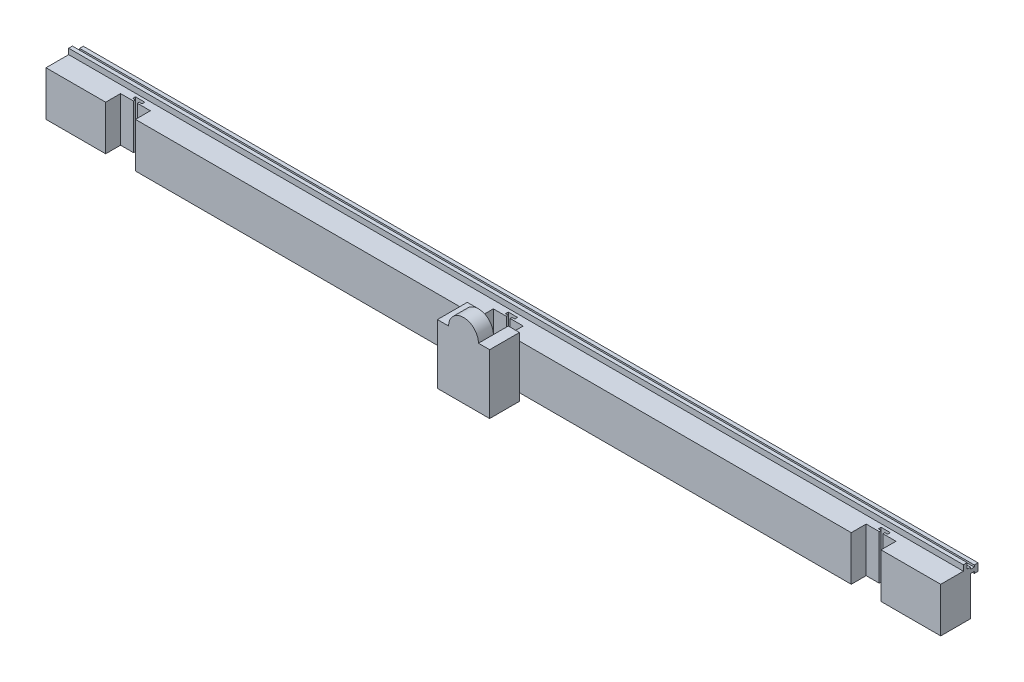
SolidWorks part; units mm, degrees
material "Plain Carbon Steel"
ref_plane "Front Plane" through (0, 0, 0) normal (0, 0, 1) x (1, 0, 0)
ref_plane "Top Plane" through (0, 0, 0) normal (0, 1, 0) x (1, 0, 0)
ref_plane "Right Plane" through (0, 0, 0) normal (1, 0, 0) x (0, 0, -1)
sketch "Sketch2" plane through (0, 0, 0) normal (0, 0, 1) x (1, 0, 0)
  line L1 (-3048, -152.4) -> (3048, -152.4)
  line L2 (-3048, -152.4) -> (-3048, 152.4)
  line L3 (-3048, 152.4) -> (3048, 152.4)
  line L4 (3048, -152.4) -> (3048, 152.4)
  line L5 (-3048, -152.4) -> (3048, 152.4) construction
  line L6 (-3048, 152.4) -> (3048, -152.4) construction
  point P0 (0, 0)
  dimension "D1" = 6096
  dimension "D2" = 304.8
extrude "Boss-Extrude1" add sketch "Sketch2" against normal blind 203.2
sketch "Sketch4" plane through (0, 152.4, 0) normal (0, 1, 0) x (1, 0, 0)
  line L0 (3048, 0) -> (-3048, 0) construction
  line L1 (-75.8517, 0) -> (75.8517, 0)
  line L2 (-75.8517, 0) -> (-75.8517, 101.6)
  line L3 (-75.8517, 101.6) -> (-12.7, 101.6)
  line L4 (75.8517, 0) -> (75.8517, 101.6)
  line L7 (-31.75, 114.3) -> (-12.7, 114.3)
  line L9 (-31.75, 114.3) -> (-31.75, 133.35)
  line L10 (-31.75, 133.35) -> (31.75, 133.35)
  line L11 (31.75, 114.3) -> (31.75, 133.35)
  line L14 (-12.7, 114.3) -> (-12.7, 101.6)
  line L16 (12.7, 114.3) -> (12.7, 101.6)
  line L17 (31.75, 114.3) -> (12.7, 114.3)
  line L18 (12.7, 101.6) -> (75.8517, 101.6)
  point P0 (0, 32.5425)
  point P11 (0, 101.6)
  dimension "D1" = 101.6
  dimension "D2" = 63.5
  dimension "D3" = 151.7034
  dimension "D5" = 19.05
extrude "Cut-Extrude1" cut sketch "Sketch4" against normal through all
pattern_linear "LPattern1" count 2 spacing 2540 along (-1, 0, 0) count 2 spacing 2540 along (1, 0, 0) of "Cut-Extrude1"
sketch "Sketch5" plane through (0, 152.4, 0) normal (0, 1, 0) x (1, 0, 0)
  line L0 (3048, 203.2) -> (3048, 0) construction
  line L1 (-3048, 179.8606) -> (3048, 179.8606)
  line L2 (-3048, 179.8606) -> (-3048, 154.4606)
  line L3 (-3048, 154.4606) -> (3048, 154.4606)
  line L4 (3048, 179.8606) -> (3048, 154.4606)
  line L5 (-3048, 179.8606) -> (3048, 154.4606) construction
  line L6 (-3048, 154.4606) -> (3048, 179.8606) construction
  point P0 (0, 167.1606)
  dimension "D1" = 25.4
  dimension "D2" = 6096
extrude "Boss-Extrude2" add sketch "Sketch5" along normal blind 38.1
sketch "Sketch7" plane through (0, 152.4, 0) normal (0, 1, 0) x (1, 0, 0)
  line L1 (-101.6, 0) -> (101.6, 0)
  line L2 (-101.6, 0) -> (-101.6, 101.6)
  line L3 (-101.6, 101.6) -> (101.6, 101.6)
  line L4 (101.6, 0) -> (101.6, 101.6)
  line L5 (-101.6, 0) -> (101.6, 101.6) construction
  line L6 (-101.6, 101.6) -> (101.6, 0) construction
  line L7 (-75.8517, 0) -> (-2464.1483, 0) construction
  point P0 (0, 50.8)
  dimension "D1" = 203.2
  dimension "D2" = 101.6
extrude "Cut-Extrude2" cut sketch "Sketch7" against normal through all
pattern_linear "LPattern2" count 2 spacing 2540 along (-1, 0, 0) count 2 spacing 2540 along (1, 0, 0) of "Cut-Extrude2"
sketch "Sketch9" plane through (-3048, 0, 0) normal (-1, 0, 0) x (0, 0, 1)
  line L0 (-228.6, 152.4) -> (-228.6, 139.7)
  line L1 (-228.6, 152.4) -> (-254, 152.4)
  line L2 (-203.2, 139.7) -> (-203.2, 114.3)
  line L3 (-228.6, 101.6) -> (-254, 101.6)
  line L4 (-254, 152.4) -> (-254, 101.6)
  line L5 (-228.6, 139.7) -> (-203.2, 139.7)
  line L6 (-228.6, 114.3) -> (-203.2, 114.3)
  line L7 (-228.6, 114.3) -> (-228.6, 101.6)
  dimension "D2" = 50.8
  dimension "D3" = 12.7
  dimension "D4" = 12.7
extrude "Boss-Extrude4" add sketch "Sketch9" against normal up to surface (6096 mm away) up to face at (3048, 85.725, -134.3803)
sketch "Sketch10" plane through (0, 152.4, 0) normal (0, 1, 0) x (1, 0, 0)
  line L0 (-101.6, 0) -> (-2438.4, 0) construction
  line L1 (-177.8, 0) -> (-101.6, 0)
  line L2 (-177.8, 0) -> (-177.8, -203.2)
  line L3 (-177.8, -203.2) -> (177.8, -203.2)
  line L4 (177.8, 0) -> (177.8, -203.2)
  line L5 (101.6, 0) -> (177.8, 0)
  line L7 (-101.6, 0) -> (-101.6, -101.6)
  line L8 (-101.6, -101.6) -> (101.6, -101.6)
  line L9 (101.6, 0) -> (101.6, -101.6)
  dimension "D1" = 355.6
  dimension "D2" = 203.2
  dimension "D3" = 177.8
  dimension "D4" = 101.6
  dimension "D5" = 203.2
extrude "Boss-Extrude5" add sketch "Sketch10" against normal blind 355.6 and the other way blind 50.8 contours L2 L3 L4 L5 L9 L8 L7 L1
sketch "Sketch11" plane through (0, 0, 203.2) normal (0, 0, 1) x (1, 0, 0)
  line L0 (-177.8, 203.2) -> (177.8, 203.2) construction
  line L1 (-101.6, 203.2) -> (101.6, 203.2)
  arc A0 (-101.6, 203.2) -> (101.6, 203.2) centre (0, 203.2) cw
extrude "Boss-Extrude6" add sketch "Sketch11" against normal blind 101.6
